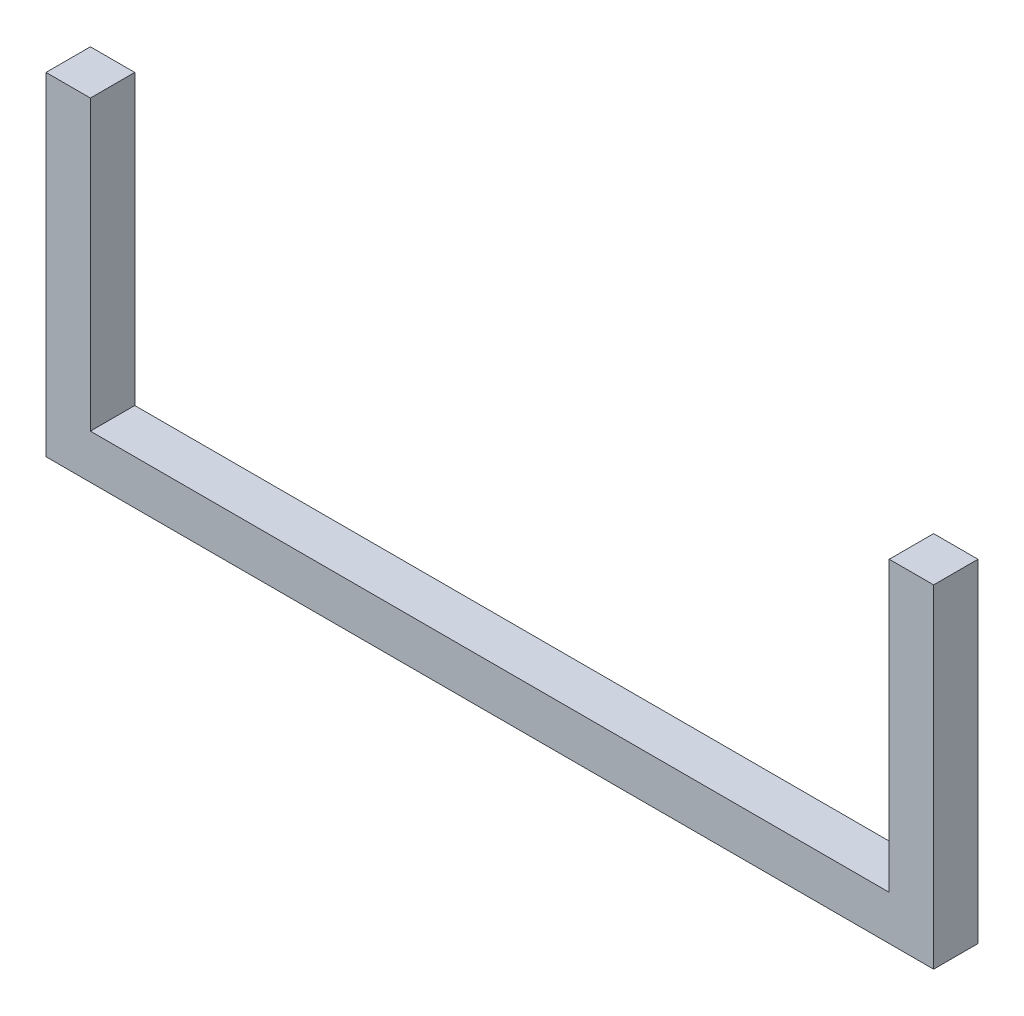
SolidWorks part; units mm, degrees
material "3.0205 (EN-AW 1200)"
ref_plane "정면" through (0, 0, 0) normal (0, 0, 1) x (1, 0, 0)
ref_plane "윗면" through (0, 0, 0) normal (0, 1, 0) x (1, 0, 0)
ref_plane "우측면" through (0, 0, 0) normal (1, 0, 0) x (0, 0, -1)
sketch "스케치2" plane through (0, 0, 0) normal (0, 0, 1) x (1, 0, 0)
  line L0 (0, 0) -> (-400, 0)
  line L1 (-400, 0) -> (-400, 150)
  line L2 (-400, 150) -> (-380, 150)
  line L3 (-380, 150) -> (-380, 20)
  line L4 (-380, 20) -> (-20, 20)
  line L5 (-20, 20) -> (-20, 150)
  line L6 (-20, 150) -> (0, 150)
  line L7 (0, 150) -> (0, 0)
  dimension "D1" = 400
  dimension "D2" = 150
  dimension "D3" = 20
  dimension "D4" = 20
  dimension "D5" = 20
  dimension "D6" = 150
extrude "보스-돌출1" add sketch "스케치2" along normal blind 20
